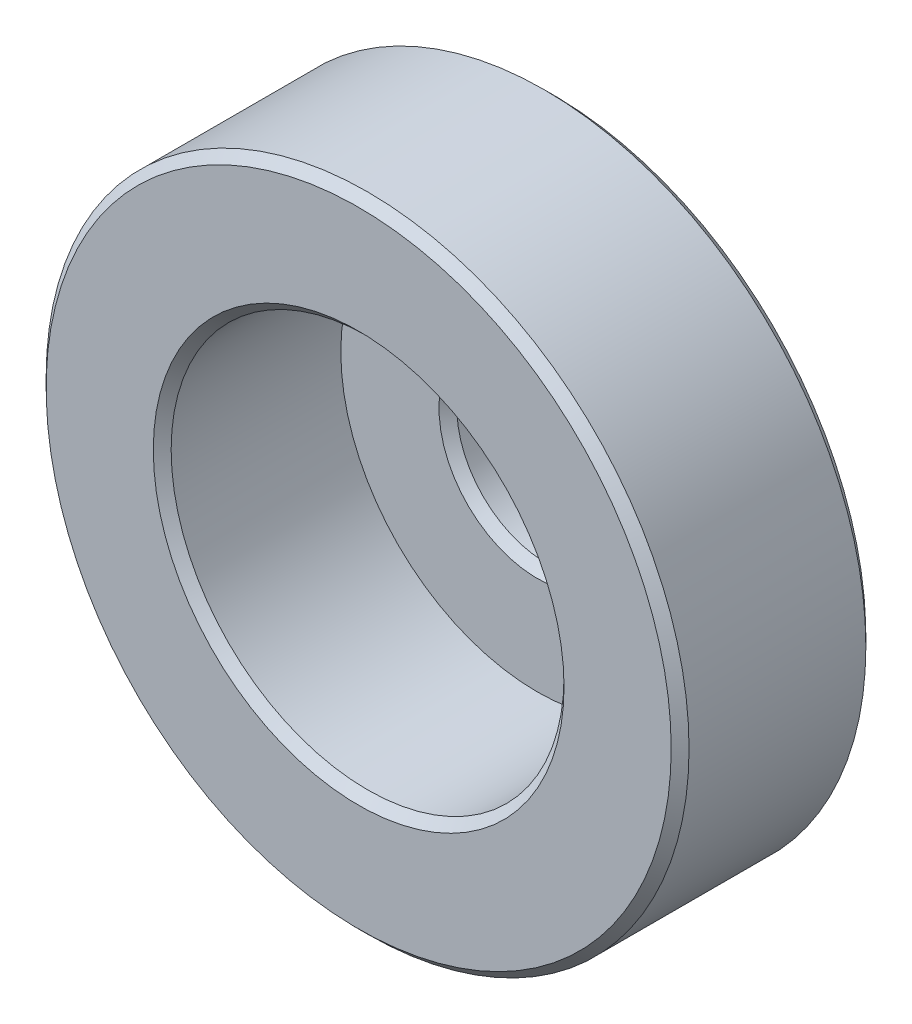
SolidWorks part; units mm, degrees
ref_plane "Front Plane" through (0, 0, 0) normal (0, 0, 1) x (1, 0, 0)
ref_plane "Top Plane" through (0, 0, 0) normal (0, 1, 0) x (1, 0, 0)
ref_plane "Right Plane" through (0, 0, 0) normal (1, 0, 0) x (0, 0, -1)
sketch "Sketch2" plane through (0, 0, 0) normal (0, 1, 0) x (1, 0, 0)
  line L0 (0, 0) -> (0, -15.4) construction
  line L1 (0, 0) -> (-18, 0) construction
  line L2 (-18, 0) -> (-18, -15.4) construction
  line L3 (-18, -15.4) -> (0, -15.4) construction
  line L4 (-11.5, 0) -> (-11.5, -15.4) construction
  line L5 (0, -4.5) -> (-18, -4.5) construction
  line L6 (-5, 0) -> (-5, -15.4) construction
  line L7 (-18, -4.5) -> (-11, -4.5)
  line L8 (-11, -4.5) -> (-11, 0)
  line L9 (-11, 0) -> (-5, 0)
  line L10 (-18, -4.5) -> (-18, -15.4)
  line L11 (-11, 0) -> (-11, -15.4) construction
  line L12 (-18, -5.4) -> (0, -5.4) construction
  line L13 (-18, -15.4) -> (-11, -15.4)
  line L14 (-11, -15.4) -> (-11, -5.4)
  line L15 (-11, -5.4) -> (-5, -5.4)
  line L16 (-5, -5.4) -> (-5, 0)
  dimension "D1" = 15.4
  dimension "D2" = 18
  dimension "D3" = 11.5
  dimension "D4" = 4.5
  dimension "D5" = 5
  dimension "D6" = 11
  dimension "D7" = 10
revolve "Revolve1" add sketch "Sketch2" angle 360 about L0
sketch "Sketch3" plane through (0, 0, 0) normal (0, 0, -1) x (-1, 0, 0)
  line L0 (0, 11.0121) -> (0, -11.0121) construction
  line L1 (1.25, 10.941) -> (1.25, 4.8412)
  line L2 (-1.25, 10.941) -> (-1.25, 4.8412)
  line L3 (1.25, -4.8412) -> (1.25, -10.941)
  line L4 (-1.25, -4.8412) -> (-1.25, -10.941)
  arc A0 (-1.25, -10.941) -> (1.25, -10.941) centre (0, 0) ccw
  arc A1 (-1.25, -4.8412) -> (1.25, -4.8412) centre (0, 0) ccw
  arc A2 (1.25, 4.8412) -> (-1.25, 4.8412) centre (0, 0) ccw
  arc A3 (1.25, 10.941) -> (-1.25, 10.941) centre (0, 0) ccw
  dimension "D1" = 1.25
extrude "Cut-Extrude1" cut sketch "Sketch3" against normal blind 1.5
chamfer "Chamfer1" distance 0.5 angle 45 6 edges at (-5, 0, 5.4) (-11, 0, 15.4) (-18, 0, 15.4) (-18, 0, 4.5) (-11, 0, 0) (11, 0, 0)
